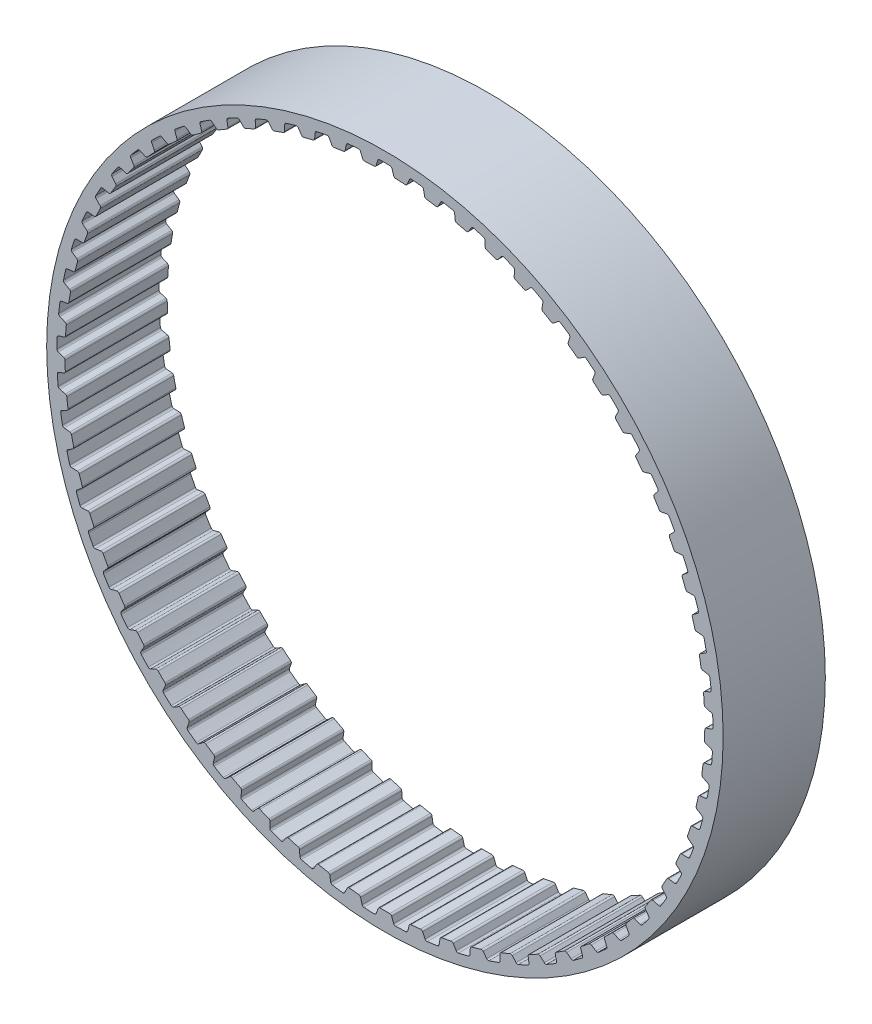
SolidWorks part; units mm, degrees
ref_plane "Front Plane" through (0, 0, 0) normal (0, 0, 1) x (1, 0, 0)
ref_plane "Top Plane" through (0, 0, 0) normal (0, 1, 0) x (1, 0, 0)
ref_plane "Right Plane" through (0, 0, 0) normal (1, 0, 0) x (0, 0, -1)
sketch "Sketch1" plane through (0, 0, 0) normal (0, 0, 1) x (1, 0, 0)
  line L0 (0, 0) -> (-0.9604, 19.855) construction
  line L1 (0, 0) -> (0.9604, 19.855) construction
  line L2 (0.9604, 19.855) -> (-0.9604, 19.855) construction
  line L3 (0.9604, 19.855) -> (-0.9604, 19.855) construction
  circle A0 centre (0, 0) radius 21.0212
  circle A1 centre (0, 0) radius 19.8782
  circle A2 centre (0, 0) radius 20.3862 construction
  dimension "OD" = 42.0424
  dimension "Angle Distance" = 5.538
  dimension "hs" = 1.143
  dimension "ht" = 0.508
extrude "Boss-Extrude1" add sketch "Sketch1" along normal mid plane 6.35
sketch "Sketch2" plane through (0, 0, 0) normal (0, 0, 1) x (1, 0, 0)
  line L1 (0, 21.0212) -> (0, 0) construction
  line L2 (-1.016, 20.1279) -> (1.016, 20.1279) construction
  line L4 (-0.5706, 19.8738) -> (-1.3501, 19.8361)
  line L5 (-0.5706, 19.8738) -> (-0.413, 20.382)
  line L6 (-1.3501, 19.8361) -> (-1.556, 20.3267)
  line L7 (0, 0) -> (-0.9604, 19.855) construction
  line L8 (-0.413, 20.382) -> (-1.556, 20.3267) construction
  line L9 (0.413, 20.382) -> (1.556, 20.3267) construction
  line L10 (1.3501, 19.8361) -> (1.556, 20.3267)
  line L11 (0.5706, 19.8738) -> (0.413, 20.382)
  line L12 (0.5706, 19.8738) -> (1.3501, 19.8361)
  line L13 (0, 0) -> (8.0445, 19.4211) construction
  line L14 (-1.016, 20.1279) -> (-3.0377, 19.9233) construction
  line L15 (-2.0268, 20.0256) -> (0, 0) construction
  line L16 (-3.0377, 19.9233) -> (-2.9962, 19.6511) construction
  circle A0 centre (0, 0) radius 20.3862 construction
  circle A1 centre (0, 0) radius 20.3862
  circle A2 centre (0, 0) radius 20.1279 construction
  circle A4 centre (0, 0) radius 21.0212 construction
  circle A5 centre (0, 0) radius 19.8782 construction
  point P16 (-0.4918, 20.1279)
  point P20 (0, 20.1279)
  dimension "D1" = 22.5
  dimension "bt" = 1.143
  dimension "b" = 40
  dimension "Pitch" = 2.032
sketch "Sketch3" plane through (0, 0, 0) normal (0, 0, 1) x (1, 0, 0)
  line L0 (-0.6621, 19.8672) -> (0.6621, 19.8672)
  line L2 (-0.5706, 19.8738) -> (-0.413, 20.382) construction
  line L3 (0.5706, 19.8738) -> (0.413, 20.382) construction
  line L5 (-0.545, 19.9565) -> (-0.4402, 20.2943)
  line L7 (0.545, 19.9565) -> (0.4402, 20.2943)
  arc A0 (0.545, 19.9565) -> (0.6621, 19.8672) centre (0.6663, 19.9941) ccw
  circle A1 centre (0, 0) radius 20.3862 construction
  arc A2 (0.3209, 20.3837) -> (-0.3209, 20.3837) centre (0, 0) ccw
  arc A3 (-0.545, 19.9565) -> (-0.6621, 19.8672) centre (-0.6663, 19.9941) cw
  arc A4 (0.4402, 20.2943) -> (0.3209, 20.3837) centre (0.3189, 20.2567) ccw
  arc A5 (-0.4402, 20.2943) -> (-0.3209, 20.3837) centre (-0.3189, 20.2567) cw
  circle A6 centre (0, 0) radius 19.8782 construction
  arc A7 (-0.6621, 19.8672) -> (0.6621, 19.8672) centre (0, 0) ccw construction
  dimension "ra" = 0.127
  dimension "rr" = 0.127
extrude "Cut-Extrude1" cut sketch "Sketch3" against normal mid plane 6.35
pattern_circular "CirPattern1" count 65 over 360 about axis through (0, 0, 0) along (0, 0, 1) of "Cut-Extrude1"
equation "\"D1@Cut-Extrude1\" = \"Width@Boss-Extrude1\""
